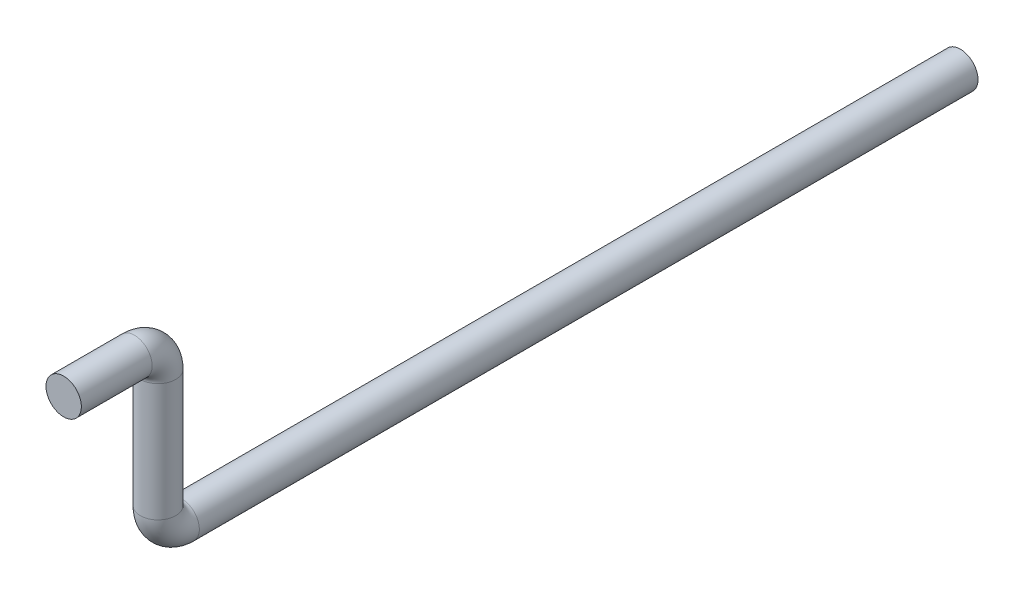
SolidWorks part; units mm, degrees
ref_plane "Alzado" through (0, 0, 0) normal (0, 0, 1) x (1, 0, 0)
ref_plane "Planta" through (0, 0, 0) normal (0, 1, 0) x (1, 0, 0)
ref_plane "Vista lateral" through (0, 0, 0) normal (1, 0, 0) x (0, 0, -1)
sketch "Croquis1" plane through (0, 0, 0) normal (0, 0, 1) x (1, 0, 0)
  circle A0 centre (0, 0) radius 7.5
  dimension "D1" = 15
sketch3d "Croquis3D1"
  line L0 (0, 0, 0) -> (0, 0, 30)
  line L1 (0, 10, 40) -> (0, 60, 40)
  line L2 (0, 70, 50) -> (0, 70, 80)
  arc A0 (0, 0, 30) -> (0, 10, 40) centre (0, 10, 30) ccw
  arc A1 (0, 60, 40) -> (0, 70, 50) centre (0, 60, 50) ccw
  point P7 (0, 0, 40)
  point P8 (-10, 10, 30)
  point P11 (0, 70, 40)
  point P12 (10, 60, 50)
  dimension "D4" = 10
  dimension "D1" = 40
  dimension "D2" = 40
  dimension "D3" = 70
sweep "Barrer1" add profiles "Croquis1" path "Croquis3D1"
sketch "Croquis2" plane through (0, 0, 0) normal (0, 0, -1) x (-1, 0, 0)
  circle A0 centre (0, 0) radius 7.5
extrude "Saliente-Extruir1" add sketch "Croquis2" along normal blind 300
